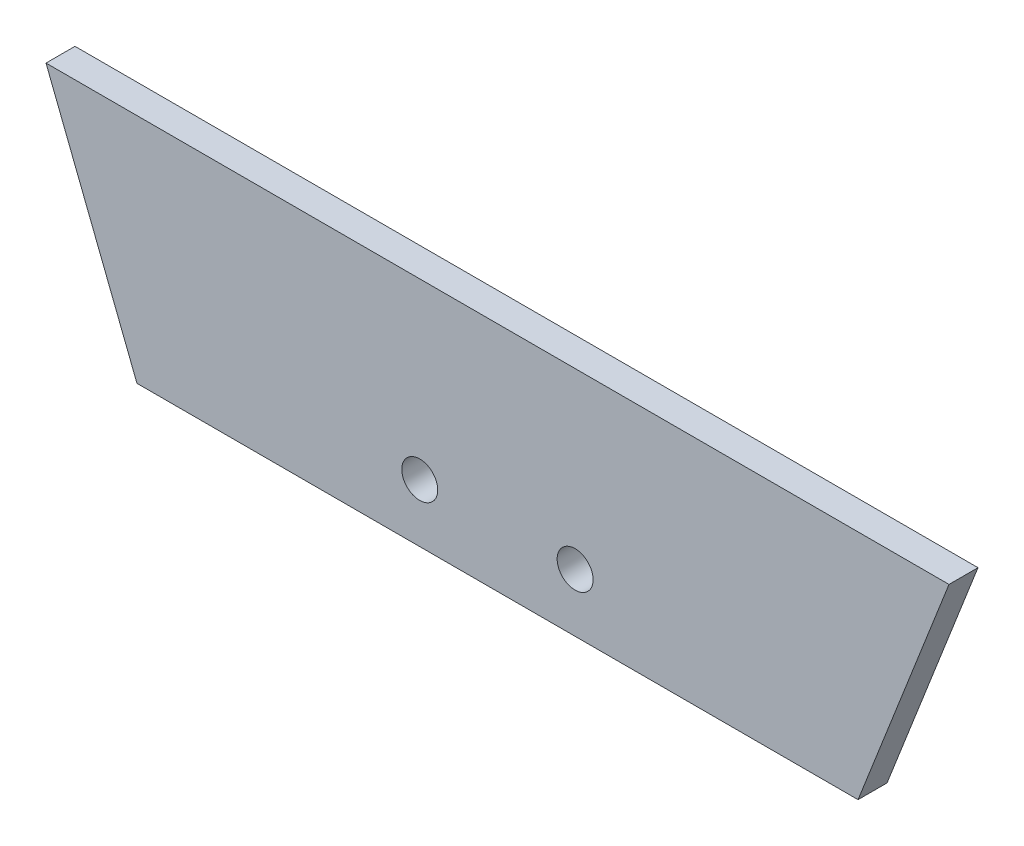
SolidWorks part; units mm, degrees
ref_plane "Front Plane" through (0, 0, 0) normal (0, 0, 1) x (1, 0, 0)
ref_plane "Top Plane" through (0, 0, 0) normal (0, 1, 0) x (1, 0, 0)
ref_plane "Right Plane" through (0, 0, 0) normal (1, 0, 0) x (0, 0, -1)
sketch "Sketch1" plane through (0, 0, 0) normal (0, 0, 1) x (1, 0, 0)
  line L0 (0, 0) -> (118.11, 0) construction
  line L1 (-63.754, 162.56) -> (181.864, 162.56) construction
  line L2 (-63.754, 162.56) -> (0, 0) construction
  line L3 (181.864, 162.56) -> (118.11, 0) construction
  point P5 (59.055, 162.56)
  point P6 (59.055, 0)
  dimension "D1" = 118.11
  dimension "D2" = 245.618
  dimension "D3" = 162.56
sketch "Sketch2" plane through (0, 0, 0) normal (0, 0, 1) x (1, 0, 0)
  line L0 (-39.8462, 101.6) -> (157.9562, 101.6)
  line L1 (-63.754, 162.56) -> (0, 0) construction
  line L2 (181.864, 162.56) -> (118.11, 0) construction
  line L6 (157.9562, 101.6) -> (138.0331, 50.8)
  line L7 (0, 0) -> (118.11, 0) construction
  line L8 (-19.9231, 50.8) -> (138.0331, 50.8)
  line L9 (-39.8462, 101.6) -> (-19.9231, 50.8)
  dimension "D1" = 101.6
  dimension "D2" = 50.8
extrude "Boss-Extrude2" add sketch "Sketch2" along normal blind 6.35
sketch "Sketch3" plane through (0, 0, 6.35) normal (0, 0, 1) x (1, 0, 0)
  line L0 (42.0211, 63.5) -> (76.0571, 63.5) construction
  line L2 (-19.9231, 50.8) -> (138.0331, 50.8) construction
  circle A0 centre (42.0211, 63.5) radius 3.937
  circle A1 centre (76.0571, 63.5) radius 3.937
  point P6 (59.0391, 63.5)
  dimension "D1" = 7.874
  dimension "D2" = 7.874
  dimension "D3" = 34.036
  dimension "D4" = 78.994
  dimension "D5" = 12.7
extrude "Cut-Extrude1" cut sketch "Sketch3" against normal blind 6.35
